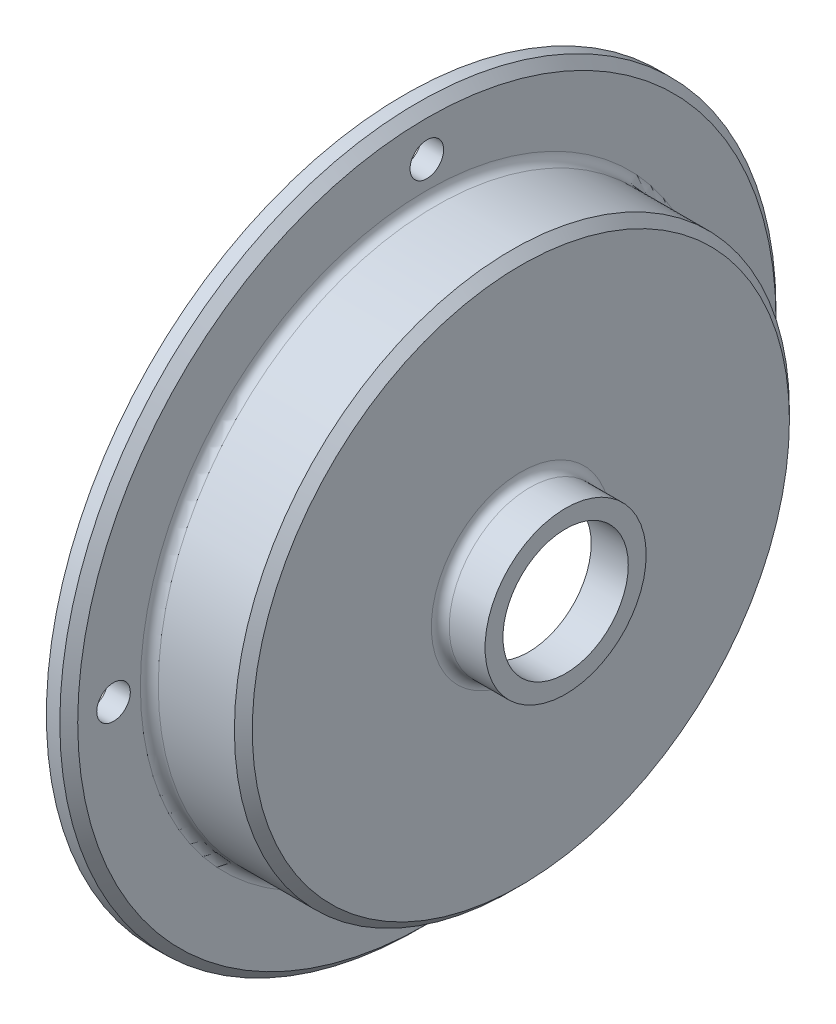
SolidWorks part; units mm, degrees
ref_plane "Front Plane" through (0, 0, 0) normal (0, 0, 1) x (1, 0, 0)
ref_plane "Top Plane" through (0, 0, 0) normal (0, 1, 0) x (1, 0, 0)
ref_plane "Right Plane" through (0, 0, 0) normal (1, 0, 0) x (0, 0, -1)
sketch "Sketch1" plane through (0, 0, 0) normal (0, 0, 1) x (1, 0, 0)
  line L1 (18.9358, 0) -> (-21.2579, 0) construction
  line L2 (-17.4934, -39.37) -> (-17.4934, -50.8)
  line L3 (-17.4934, -50.8) -> (-14.3184, -50.8)
  line L4 (-14.3184, -50.8) -> (-14.3184, -39.37)
  line L7 (-14.3184, -39.37) -> (5.3666, -39.37)
  line L9 (0.1043, -8.89) -> (5.3666, -8.89)
  line L10 (-17.4934, -39.37) -> (0.1043, -8.89)
  line L11 (5.3666, -8.89) -> (5.3666, -39.37)
  dimension "D1" = 3.175
  dimension "D2" = 50.8
  dimension "D3" = 30
  dimension "D4" = 19.685
  dimension "D5" = 39.37
  dimension "D7" = 8.89
revolve "Revolve1" add sketch "Sketch1" angle 360 about L1
fillet "Fillet1" radius 1.27 1 edges at (-14.3184, 0, -39.37)
sketch "Sketch3" plane through (5.3666, 0, 0) normal (1, 0, 0) x (0, 0, -1)
  circle A0 centre (0, 0) radius 39.37
  circle A1 centre (0, 0) radius 11.43
  dimension "D1" = 78.74
  dimension "D2" = 22.86
extrude "Cut-Extrude1" cut sketch "Sketch3" against normal blind 6.35
chamfer "Chamfer1" distance 1.27 angle 45 2 edges at (-0.9834, 0, -39.37) (-14.3184, 0, -50.8)
fillet "Fillet2" radius 1.27 1 edges at (-0.9834, 0, -11.43)
hole_wizard "3/16 (0.1875) Diameter Hole1" positions "Sketch4" profile "Sketch5" hole size "3/16" standard "ANSI Inch"
sketch "Sketch4" plane through (-17.4934, 0, 0) normal (-1, 0, 0) x (0, 0, 1)
  point P0 (-44.45, 0)
  point P2 (0, 44.45)
  point P4 (44.45, 0)
  point P6 (0, -44.45)
  point P14 (0, 0)
  point P15 (0, 0)
  point P16 (0, 0)
  point P17 (0, 0)
  point P18 (0, 0)
  dimension "D1" = 44.45
  dimension "D2" = 44.45
  dimension "D3" = 44.45
  dimension "D4" = 44.45
sketch "Sketch5" plane through (-17.4934, 0, -44.45) normal (0, 1, 0) x (0, 0, 1)
  line L0 (0, 0) -> (0, 15.4008)
  line L1 (0, 15.4008) -> (2.3812, 13.97)
  line L2 (2.3812, 13.97) -> (2.3812, 0)
  line L5 (2.3812, 0) -> (0, 0)
  line L10 (0, 15.4008) -> (-2.3812, 13.97) construction
  line L11 (0, -6.35) -> (0, 107.95) construction
  dimension "Hole Dia." = 4.7625
  dimension "Hole Depth" = 13.97
  dimension "Drill Angle" = 118
